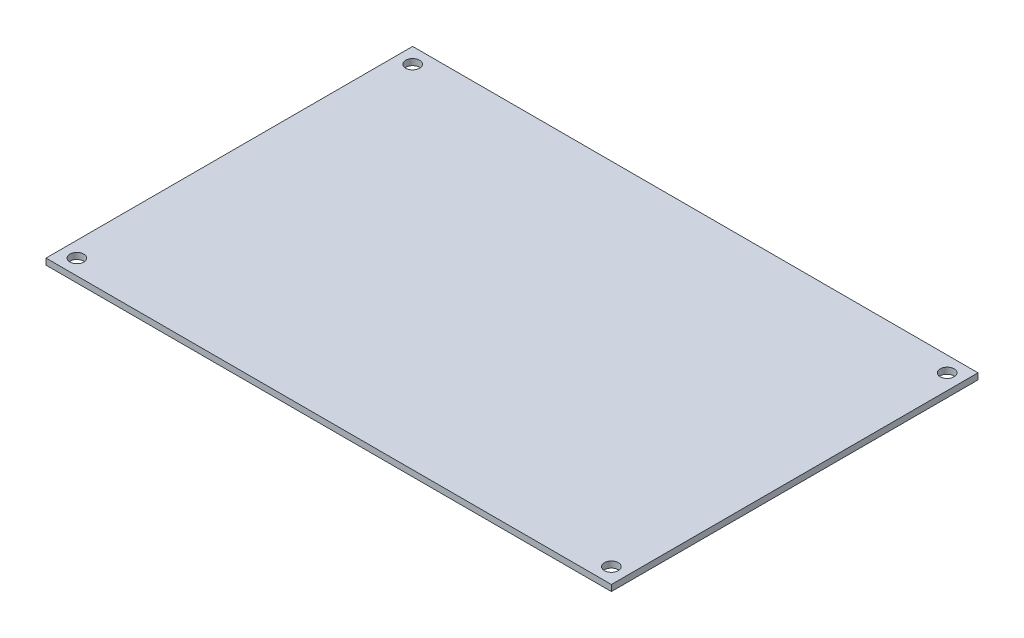
SolidWorks part; units mm, degrees
ref_plane "Front" through (0, 0, 0) normal (0, 0, 1) x (1, 0, 0)
ref_plane "Top" through (0, 0, 0) normal (0, 1, 0) x (1, 0, 0)
ref_plane "Right" through (0, 0, 0) normal (1, 0, 0) x (0, 0, -1)
sketch "Sketch1"
sketch "Sketch2" plane through (0, 0, 0) normal (0, 1, 0) x (1, 0, 0)
  line L0 (0, 82.799) -> (0, 0) construction
  line L1 (-73.25, 47.5) -> (73.25, 47.5)
  line L2 (-73.25, 47.5) -> (-73.25, -47.5)
  line L3 (-73.25, -47.5) -> (73.25, -47.5)
  line L4 (73.25, 47.5) -> (73.25, -47.5)
  line L5 (0, 0) -> (105.0232, 0) construction
  circle A0 centre (-69.25, 43.5) radius 1.8
  circle A1 centre (69.25, 43.5) radius 1.8
  circle A2 centre (69.25, -43.5) radius 1.8
  circle A3 centre (-69.25, -43.5) radius 1.8
  dimension "D3" = 3.6
  dimension "D1" = 146.5
  dimension "D2" = 95
  dimension "D4" = 4
  dimension "D5" = 4
extrude "Boss-Extrude1" add sketch "Sketch2" against normal blind 1.6
